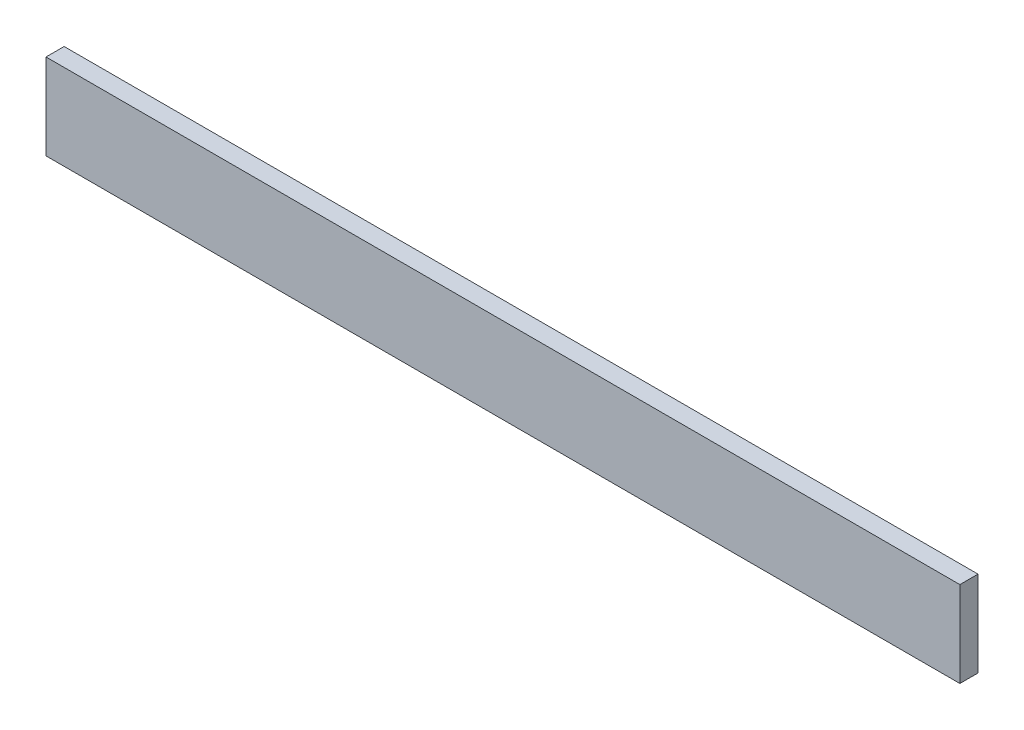
SolidWorks part; units mm, degrees
ref_plane "Front Plane" through (0, 0, 0) normal (0, 0, 1) x (1, 0, 0)
ref_plane "Top Plane" through (0, 0, 0) normal (0, 1, 0) x (1, 0, 0)
ref_plane "Right Plane" through (0, 0, 0) normal (1, 0, 0) x (0, 0, -1)
sketch "Sketch1" plane through (0, 0, 0) normal (0, 0, 1) x (1, 0, 0)
  line L1 (-80, 7.5) -> (80, 7.5)
  line L2 (-80, 7.5) -> (-80, -7.5)
  line L3 (-80, -7.5) -> (80, -7.5)
  line L4 (80, 7.5) -> (80, -7.5)
  line L5 (-80, 7.5) -> (80, -7.5) construction
  line L6 (-80, -7.5) -> (80, 7.5) construction
  point P0 (0, 0)
  dimension "D1" = 160
  dimension "D2" = 15
extrude "Boss-Extrude1" add sketch "Sketch1" along normal blind 3.175
sketch "Sketch2" plane through (0, 0, 3.175) normal (0, 0, 1) x (1, 0, 0)
  line L0 (-80, 0) -> (80, 0) construction
  line L1 (-80, 7.5) -> (-80, -7.5) construction
  line L2 (80, -7.5) -> (80, 7.5) construction
  circle A0 centre (-73.25, 0) radius 3.3295
  circle A1 centre (73.25, 0) radius 2.9567
  dimension "D1" = 73.25
  dimension "D2" = 73.25
